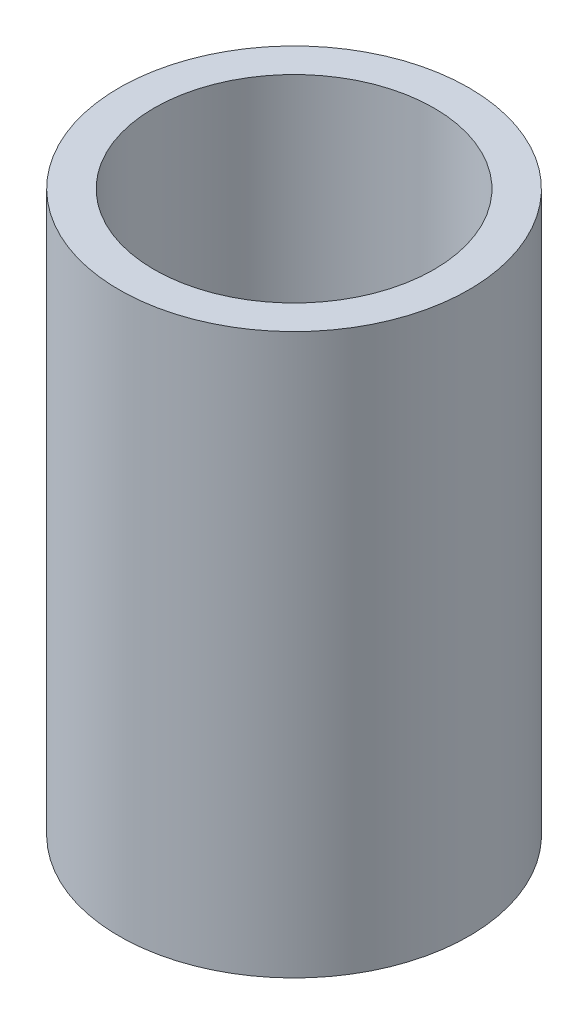
SolidWorks part; units mm, degrees
ref_plane "Front Plane" through (0, 0, 0) normal (0, 0, 1) x (1, 0, 0)
ref_plane "Top Plane" through (0, 0, 0) normal (0, 1, 0) x (1, 0, 0)
ref_plane "Right Plane" through (0, 0, 0) normal (1, 0, 0) x (0, 0, -1)
sketch "Sketch1" plane through (0, 0, 0) normal (0, 0, 1) x (1, 0, 0)
  line L0 (0, 0) -> (0, 20.8973) construction
  line L2 (6, 0) -> (7.5, 0)
  line L3 (6, 0) -> (6, 24)
  line L4 (6, 24) -> (7.5, 24)
  line L5 (7.5, 0) -> (7.5, 24)
  point P7 (0, 0)
  dimension "D1" = 24
  dimension "D2" = 6
  dimension "D3" = 7.5
revolve "Revolve1" add sketch "Sketch1" angle 360 about L0
